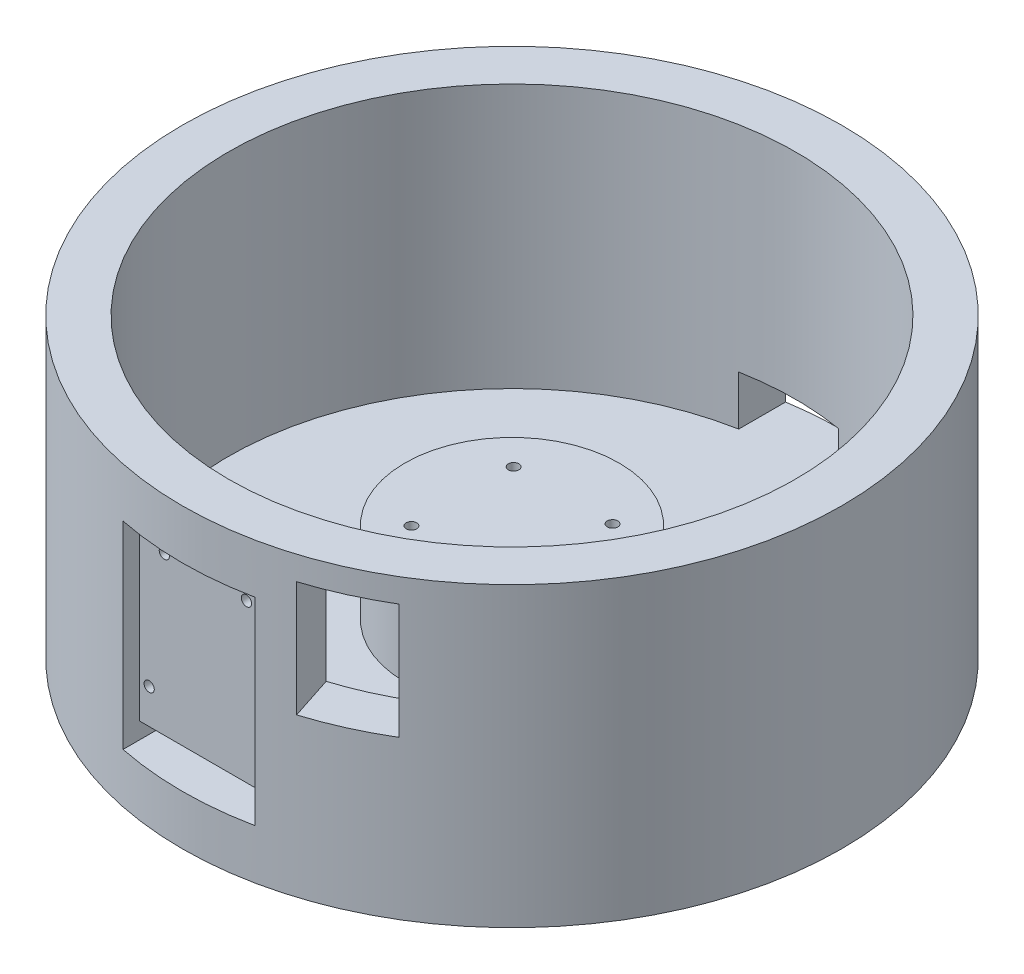
SolidWorks part; units mm, degrees
material "ABS"
ref_plane "Front Plane" through (0, 0, 0) normal (0, 0, 1) x (1, 0, 0)
ref_plane "Top Plane" through (0, 0, 0) normal (0, 1, 0) x (1, 0, 0)
ref_plane "Right Plane" through (0, 0, 0) normal (1, 0, 0) x (0, 0, -1)
sketch "Sketch1" plane through (0, 0, 0) normal (0, 1, 0) x (1, 0, 0)
  circle A1 centre (0, 0) radius 100
extrude "Boss-Extrude3" add sketch "Sketch1" along normal blind 90
ref_plane "Plane1" through (0, 0, 105) normal (0, 0, 1) x (1, 0, 0)
sketch "Sketch4" plane through (0, 0, 105) normal (0, 0, 1) x (1, 0, 0)
  line L26 (-20, 75) -> (20, 75)
  line L27 (-20, 75) -> (-20, 15)
  line L28 (-20, 15) -> (20, 15)
  line L29 (20, 75) -> (20, 15)
  line L30 (-20, 75) -> (20, 15) construction
  line L31 (-20, 15) -> (20, 75) construction
  point P5 (0, 45)
  dimension "D1" = 60
  dimension "D2" = 40
  dimension "D3" = 45
extrude "Cut-Extrude2" cut sketch "Sketch4" along normal blind 26 and the other way blind 12
sketch "Sketch12" plane through (0, 0, 0) normal (0, -1, 0) x (1, 0, 0)
  circle A1 centre (0, 0) radius 100
  circle A2 centre (0, 0) radius 100
  dimension "D1" = 0
extrude "Boss-Extrude4" add sketch "Sketch12" along normal blind 0.1
sketch "Sketch13" plane through (0, 90, 0) normal (0, 1, 0) x (1, 0, 0)
  circle A0 centre (0, 0) radius 86
extrude "Cut-Extrude8" cut sketch "Sketch13" against normal blind 80 contours A0
sketch "Sketch18" plane through (0, 10, 0) normal (0, 1, 0) x (1, 0, 0)
  circle A0 centre (0, 0) radius 32.5
  dimension "D1" = 65
extrude "Boss-Extrude5" add sketch "Sketch18" along normal blind 25
sketch "Sketch16" plane through (0, -0.1, 0) normal (0, -1, 0) x (1, 0, 0)
  line L0 (0, 0) -> (-8.9936, 0) construction
  line L1 (0, 0) -> (0, 9.8047) construction
  circle A2 centre (-15, 15.5) radius 1.6
  circle A5 centre (15, 15.5) radius 1.6
  circle A6 centre (15, -15.5) radius 1.6
  circle A7 centre (-15, -15.5) radius 1.6
  dimension "D3" = 3.2
  dimension "D1" = 15.5
  dimension "D2" = 15
extrude "Cut-Extrude11" cut sketch "Sketch16" against normal through all
sketch "Sketch17" plane through (0, -0.1, 0) normal (0, -1, 0) x (1, 0, 0)
  circle A0 centre (-15, 15.5) radius 3
  circle A1 centre (15, 15.5) radius 3
  circle A2 centre (-15, -15.5) radius 3
  circle A3 centre (15, -15.5) radius 3
  dimension "D1" = 6
  dimension "D2" = 6
  dimension "D3" = 6
  dimension "D4" = 6
extrude "Cut-Extrude12" cut sketch "Sketch17" against normal blind 30
sketch "Sketch19" plane through (0, -0.1, 0) normal (0, -1, 0) x (1, 0, 0)
  circle A0 centre (0, 0) radius 30
  dimension "D1" = 60
extrude "Cut-Extrude13" cut sketch "Sketch19" against normal blind 25 contours A0
sketch "Sketch20" plane through (0, 0, 93) normal (0, 0, 1) x (1, 0, 0)
  line L0 (20, 75) -> (20, 15) construction
  line L1 (-20, 15) -> (20, 15)
  line L2 (-20, 15) -> (-20, 20)
  line L3 (-20, 20) -> (20, 20)
  line L4 (20, 15) -> (20, 20)
  dimension "D1" = 5
extrude "Cut-Extrude14" cut sketch "Sketch20" against normal blind 25
sketch "Sketch21" plane through (0, 0, 93) normal (0, 0, 1) x (1, 0, 0)
  line L0 (20, 75) -> (-20, 75) construction
  circle A0 centre (12.45, 67.8) radius 1.55
  circle A1 centre (-12.45, 67.8) radius 1.55
  circle A2 centre (-17.05, 30.54) radius 1.55
  circle A3 centre (17.05, 30.54) radius 1.55
  dimension "D3" = 3.1
  dimension "D4" = 3.1
  dimension "D9" = 3.1
  dimension "D10" = 3.1
  dimension "D1" = 12.45
  dimension "D2" = 24.9
  dimension "D5" = 7.2
  dimension "D6" = 7.2
  dimension "D7" = 17.05
  dimension "D8" = 17.05
  dimension "D11" = 37.26
  dimension "D12" = 37.26
extrude "Cut-Extrude15" cut sketch "Sketch21" against normal blind 25
ref_plane "Plane2" through (22.2041, 47.7941, -296.4042) normal (0, 1, 0) x (1, 0, 0)
sketch "Sketch22" plane through (22.2041, 47.7941, -296.4042) normal (0, 1, 0) x (1, 0, 0)
  line L0 (-6.7919, -346.9591) -> (12.405, -405.7625)
  line L1 (-6.7919, -346.9591) -> (3.9537, -342.2121)
  line L2 (3.9537, -342.2121) -> (37.058, -394.3842)
  line L3 (12.405, -405.7625) -> (37.058, -394.3842)
extrude "Cut-Extrude16" cut sketch "Sketch22" along normal blind 35
ref_plane "Plane3" through (0, 0, -100) normal (0, 0, 1) x (1, 0, 0)
sketch "Sketch23" plane through (0, 0, -100) normal (0, 0, 1) x (1, 0, 0)
  line L1 (14.2214, 25) -> (-15.7786, 25)
  line L2 (14.2214, 25) -> (14.2214, 10)
  line L3 (14.2214, 10) -> (-15.7786, 10)
  line L4 (-15.7786, 25) -> (-15.7786, 10)
  line L5 (-100, -0.1) -> (100, -0.1) construction
  dimension "D1" = 30
  dimension "D2" = 15
  dimension "D3" = 10.1
extrude "Cut-Extrude17" cut sketch "Sketch23" along normal blind 20
